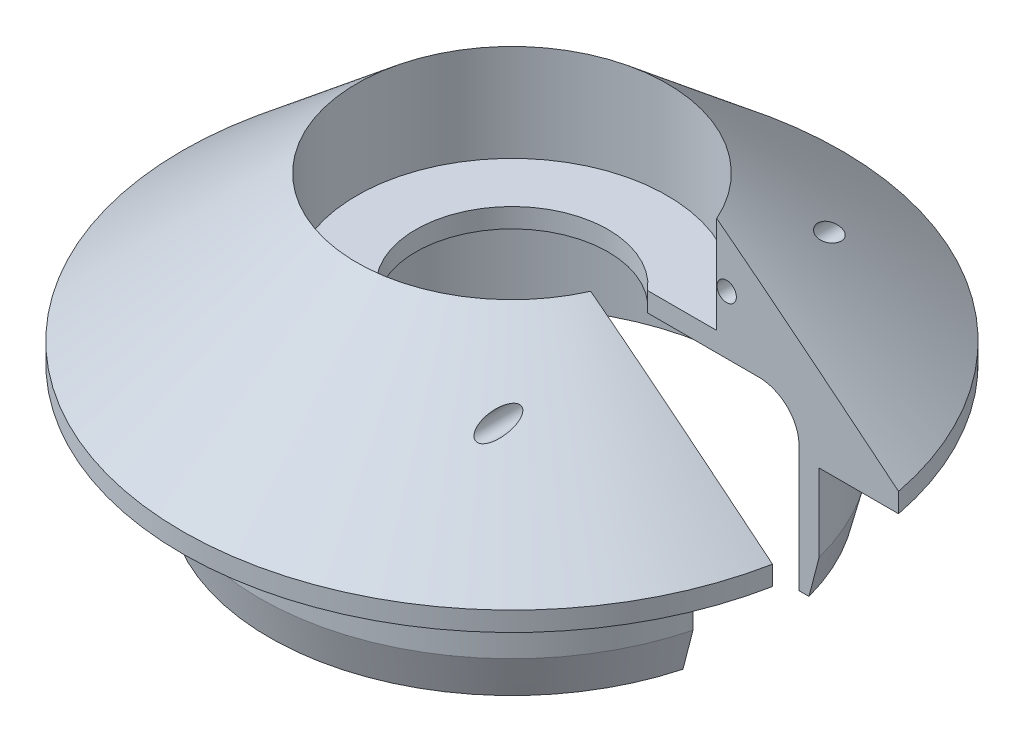
SolidWorks part; units mm, degrees
material "6061 Alloy"
ref_plane "Front" through (0, 0, 0) normal (0, 0, 1) x (1, 0, 0)
ref_plane "Top" through (0, 0, 0) normal (0, 1, 0) x (1, 0, 0)
ref_plane "Right" through (0, 0, 0) normal (1, 0, 0) x (0, 0, -1)
sketch "Sketch2" plane through (0, 0, 0) normal (1, 0, 0) x (0, 0, -1)
  line L0 (0, 42.4814) -> (0, -33.1243) construction
  line L1 (12.7, 9.525) -> (12.7, 1.5875)
  line L2 (12.7, 1.5875) -> (7.874, 1.5875)
  line L3 (7.874, 1.5875) -> (7.874, 0)
  line L4 (7.874, 0) -> (15.875, 0)
  line L5 (19.05, -3.175) -> (19.05, -13.4937)
  line L6 (19.05, -13.4937) -> (19.8438, -13.4937)
  line L7 (19.8438, -13.4937) -> (20.6375, -10.3187)
  line L8 (20.6375, -10.3187) -> (20.6375, -3.9687)
  line L9 (20.6375, -3.9687) -> (26.9875, -3.9687)
  line L10 (26.9875, -3.9687) -> (26.9875, -2.3812)
  line L11 (26.9875, -2.3812) -> (12.7, 9.525)
  arc A0 (15.875, 0) -> (19.05, -3.175) centre (15.875, -3.175) cw
  point P16 (19.05, 0)
  dimension "D13" = 3.175
  dimension "D1" = 12.7
  dimension "D2" = 4.826
  dimension "D3" = 7.9375
  dimension "D4" = 20.6375
  dimension "D5" = 1.5875
  dimension "D6" = 0.7937
  dimension "D7" = 13.4937
  dimension "D8" = 1.5875
  dimension "D9" = 3.175
  dimension "D10" = 26.9875
  dimension "D11" = 1.5875
  dimension "D12" = 9.525
revolve "Revolve1" add sketch "Sketch2" angle 360 about L0
sketch "Sketch3" plane through (0, 0, 0) normal (0, 1, 0) x (1, 0, 0)
  line L1 (0, 5.1594) -> (26.9875, 5.1594)
  line L2 (0, 5.1594) -> (0, -5.1594)
  line L3 (0, -5.1594) -> (26.9875, -5.1594)
  line L4 (26.9875, 5.1594) -> (26.9875, -5.1594)
  circle A0 centre (0, 0) radius 26.9875 construction
  dimension "D1" = 10.3187
extrude "Extrude1" cut sketch "Sketch3" against normal through all and the other way through all
sketch "Sketch4" plane through (0, 0, 0) normal (0, 0, 1) x (1, 0, 0)
  line L0 (11.6048, 1.5875) -> (-12.7, 1.5875) construction
  line L1 (11.6048, 9.525) -> (11.6048, 1.5875) construction
  circle A0 centre (12.4176, 4.7625) radius 0.7937
  dimension "D1" = 1.5875
  dimension "D2" = 3.175
  dimension "D3" = 0.8128
extrude "Extrude2" cut sketch "Sketch4" against normal through all and the other way through all
